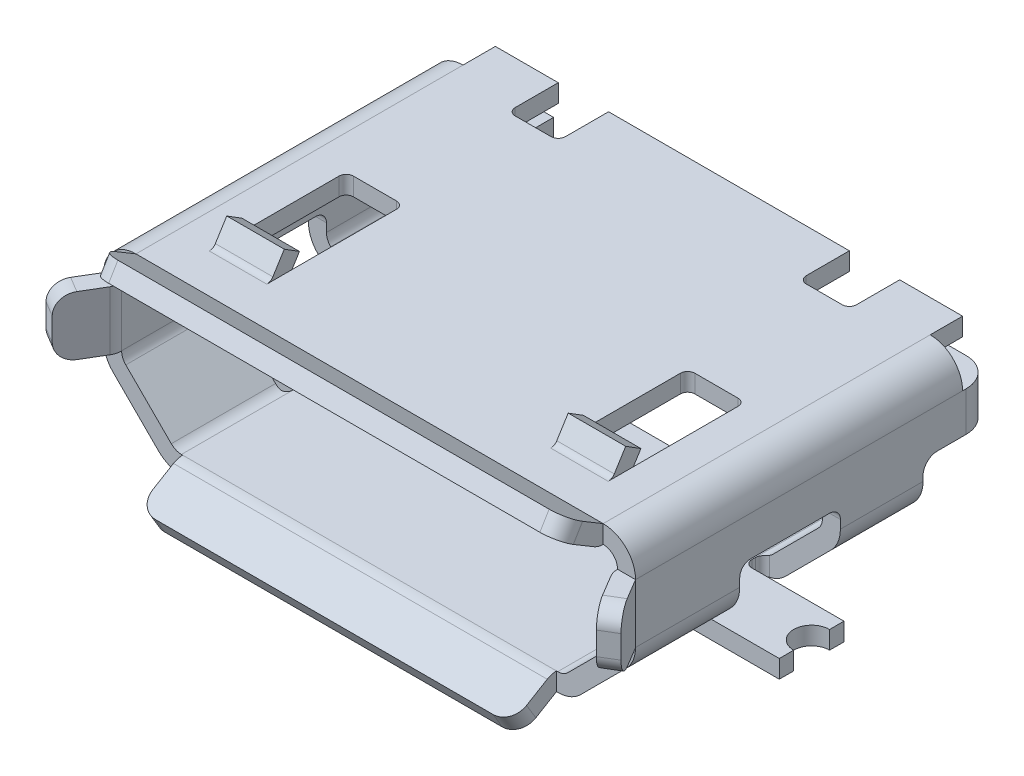
SolidWorks part; units mm, degrees
material "Pure Silver"
ref_plane "Front Plane" through (0, 0, 0) normal (0, 0, 1) x (1, 0, 0)
ref_plane "Top Plane" through (0, 0, 0) normal (0, 1, 0) x (1, 0, 0)
ref_plane "Right Plane" through (0, 0, 0) normal (1, 0, 0) x (0, 0, -1)
sketch "Sketch1" plane through (0, 0, 0) normal (0, 0, 1) x (1, 0, 0)
  line L0 (0, 0) -> (2.6172, 0)
  line L1 (55, 0) -> (-55, 0) construction
  line L2 (2.7586, 0.0586) -> (3.3914, 0.6914)
  line L3 (3.45, 0.8328) -> (3.45, 1.65)
  line L4 (3.25, 1.85) -> (-3.25, 1.85)
  line L5 (-3.45, 1.65) -> (-3.45, 0.8328)
  line L6 (-3.3914, 0.6914) -> (-2.7586, 0.0586)
  line L7 (-2.6172, 0) -> (0, 0)
  line L8 (0, -55) -> (0, 55) construction
  arc A0 (-3.25, 1.85) -> (-3.45, 1.65) centre (-3.25, 1.65) ccw
  arc A1 (-3.45, 0.8328) -> (-3.3914, 0.6914) centre (-3.25, 0.8328) ccw
  arc A2 (-2.7586, 0.0586) -> (-2.6172, 0) centre (-2.6172, 0.2) ccw
  arc A3 (2.6172, 0) -> (2.7586, 0.0586) centre (2.6172, 0.2) ccw
  arc A4 (3.3914, 0.6914) -> (3.45, 0.8328) centre (3.25, 0.8328) ccw
  arc A5 (3.45, 1.65) -> (3.25, 1.85) centre (3.25, 1.65) ccw
  point P14 (-3.45, 1.85)
  point P17 (-3.45, 0.75)
  point P20 (-2.7, 0)
  point P23 (2.7, 0)
  point P26 (3.45, 0.75)
  dimension "D7" = 0.2
  dimension "D1" = 6.9
  dimension "D2" = 3.45
  dimension "D3" = 1.85
  dimension "D4" = 1.1
  dimension "D5" = 5.4
  dimension "D6" = 2.7
extrude "Extrude-Thin1" add sketch "Sketch1" against normal blind 5 thin
ref_plane "Plane1" through (0, 1.65, 0) normal (0, 1, 0) x (1, 0, 0)
sketch "Sketch2" plane through (0, 1.65, 0) normal (0, 1, 0) x (1, 0, 0)
  line L0 (-3.7, 0) -> (-4, -0.5017)
  line L1 (-1.2925, 0) -> (1.2925, 0) construction
  line L2 (-3.7, 5) -> (-3.7, 0) construction
  line L3 (-4, -0.5017) -> (-3.7854, -0.63)
  line L4 (-3.7854, -0.63) -> (-3.4854, -0.1283)
  line L5 (-3.45, 0) -> (-3.7, 0)
  line L6 (0, -1.2925) -> (0, 1.2925) construction
  line L7 (3.7, 0) -> (4, -0.5017)
  line L9 (3.7, 5) -> (3.7, 0) construction
  line L10 (4, -0.5017) -> (3.7854, -0.63)
  line L11 (3.7854, -0.63) -> (3.4854, -0.1283)
  line L12 (3.45, 0) -> (3.7, 0)
  arc A0 (-3.4854, -0.1283) -> (-3.45, 0) centre (-3.7, 0) ccw
  arc A1 (3.4854, -0.1283) -> (3.45, 0) centre (3.7, 0) cw
  dimension "D1" = 0.25
  dimension "D2" = 0.63
  dimension "D3" = 4
  dimension "D4" = 0.25
  dimension "D5" = 0.25
  dimension "D6" = 0.63
  dimension "D7" = 4
extrude "Boss-Extrude1" add sketch "Sketch2" against normal blind 0.82
sketch "Sketch3" plane through (0, 0, 0) normal (1, 0, 0) x (0, 0, -1)
  line L0 (0, 2.1) -> (-0.5017, 2.4)
  line L1 (0, 1.6225) -> (0, -1.6225) construction
  line L2 (-0.5017, 2.4) -> (-0.63, 2.1854)
  line L3 (-0.63, 2.1854) -> (-0.1283, 1.8854)
  line L5 (5, 2.1) -> (0, 2.1) construction
  line L6 (0, 2.1) -> (0, 1.85)
  arc A0 (-0.1283, 1.8854) -> (0, 1.85) centre (0, 2.1) ccw
  dimension "D1" = 0.25
  dimension "D2" = 0.63
  dimension "D3" = 0.3
sketch "Sketch4" plane through (0, 0, 0) normal (1, 0, 0) x (0, 0, -1)
  line L0 (0, -0.25) -> (-0.5017, -0.55)
  line L1 (0, 1.6225) -> (0, -1.6225) construction
  line L2 (5, -0.25) -> (0, -0.25) construction
  line L3 (-0.5017, -0.55) -> (-0.63, -0.3354)
  line L4 (-0.63, -0.3354) -> (-0.1283, -0.0354)
  line L5 (0, 0) -> (0, -0.25)
  arc A0 (-0.1283, -0.0354) -> (0, 0) centre (0, -0.25) cw
  dimension "D1" = 0.63
  dimension "D2" = 0.3
extrude "Boss-Extrude2" add sketch "Sketch4" along normal mid plane 5.2
extrude "Boss-Extrude3" add sketch "Sketch3" along normal mid plane 6.5
fillet "Fillet1" radius 0.25 8 edges at (3.8927, 0.83, 0.5658) (3.8927, 1.65, 0.5658) (-3.8927, 0.83, 0.5658) (-3.8927, 1.65, 0.5658) (-2.6, -0.4427, 0.5658) (2.6, -0.4427, 0.5658) (3.25, 2.2927, 0.5658) (-3.25, 2.2927, 0.5658)
sketch "Sketch5" plane through (0, 0, 0) normal (0, 1, 0) x (1, 0, 0)
  line L0 (2.7172, 1.45) -> (3.7, 1.45)
  line L2 (3.7, 5) -> (3.7, 0) construction
  line L3 (3.7, 1.45) -> (3.7, 2.85)
  line L4 (3.7, 2.85) -> (2.7172, 2.85)
  line L5 (2.6172, 2.75) -> (2.6172, 1.55)
  line L6 (-3.7, 2.85) -> (-2.7172, 2.85)
  line L7 (-3.7, 5) -> (-3.7, 0) construction
  line L8 (-2.6172, 2.75) -> (-2.6172, 1.55)
  line L10 (-2.7172, 1.45) -> (-3.7, 1.45)
  line L11 (-3.7, 2.85) -> (-3.7, 1.45)
  line L12 (2.6172, 2.15) -> (3.7, 2.15) construction
  line L13 (-1.6225, 0) -> (1.6225, 0) construction
  line L14 (-2.6172, 5) -> (-2.6172, 0) construction
  line L15 (2.6172, 5) -> (2.6172, 0) construction
  arc A0 (-2.6172, 2.75) -> (-2.7172, 2.85) centre (-2.7172, 2.75) ccw
  arc A1 (2.7172, 1.45) -> (2.6172, 1.55) centre (2.7172, 1.55) cw
  arc A2 (2.7172, 2.85) -> (2.6172, 2.75) centre (2.7172, 2.75) ccw
  arc A3 (-2.6172, 1.55) -> (-2.7172, 1.45) centre (-2.7172, 1.55) cw
  dimension "D3" = 0.1
  dimension "D1" = 2.15
  dimension "D2" = 1.4
extrude "Cut-Extrude1" cut sketch "Sketch5" along normal blind 1.1 and the other way through all
fillet "Fillet2" radius 0.15 4 edges at (3.575, 1.1, -1.45) (3.575, 1.1, -2.85) (-3.575, 1.1, -2.85) (-3.575, 1.1, -1.45)
sketch "Sketch6" plane through (0, -0.25, 0) normal (0, -1, 0) x (1, 0, 0)
  line L0 (0, -1.6225) -> (0, 1.6225) construction
  line L1 (-4, -1.7) -> (4, -1.7)
  line L2 (-4, -1.7) -> (-4, -1.9)
  line L3 (-4, -2.6) -> (4, -2.6)
  line L4 (4, -1.7) -> (4, -1.9)
  line L5 (-4, -2.15) -> (4, -2.15) construction
  line L6 (1.6225, 0) -> (-1.6225, 0) construction
  line L7 (-4, -2.4) -> (-4, -2.6)
  line L8 (4, -2.4) -> (4, -2.6)
  arc A0 (-4, -2.4) -> (-4, -1.9) centre (-4, -2.15) ccw
  arc A1 (4, -1.9) -> (4, -2.4) centre (4, -2.15) ccw
  dimension "D5" = 0.5
  dimension "D1" = 8
  dimension "D2" = 4
  dimension "D3" = 2.15
  dimension "D4" = 0.9
extrude "Boss-Extrude4" add sketch "Sketch6" against normal blind 0.25
fillet "Fillet3" radius 0.1 4 edges at (2.6172, -0.125, -2.6) (2.6172, -0.125, -1.7) (-2.6172, -0.125, -1.7) (-2.6172, -0.125, -2.6)
sketch "Sketch7" plane through (0, 2.1, 0) normal (0, 1, 0) x (1, 0, 0)
  line L0 (-1.6225, 0) -> (1.6225, 0) construction
  line L1 (-2.675, 2.45) -> (-2.075, 2.45)
  line L2 (-2.775, 2.35) -> (-2.775, 0.6)
  line L3 (-2.775, 0.6) -> (-1.975, 0.6)
  line L4 (-1.975, 2.35) -> (-1.975, 0.6)
  line L5 (2.075, 2.45) -> (2.675, 2.45)
  line L6 (1.975, 2.35) -> (1.975, 0.6)
  line L7 (1.975, 0.6) -> (2.775, 0.6)
  line L8 (2.775, 2.35) -> (2.775, 0.6)
  line L9 (-2.375, 2.45) -> (-2.375, 0.6) construction
  line L10 (2.375, 2.45) -> (2.375, 0.6) construction
  line L11 (0, -1.6225) -> (0, 1.6225) construction
  arc A0 (2.675, 2.45) -> (2.775, 2.35) centre (2.675, 2.35) cw
  arc A1 (2.075, 2.45) -> (1.975, 2.35) centre (2.075, 2.35) ccw
  arc A2 (-2.675, 2.45) -> (-2.775, 2.35) centre (-2.675, 2.35) ccw
  arc A3 (-1.975, 2.35) -> (-2.075, 2.45) centre (-2.075, 2.35) ccw
  dimension "D1" = 0.1
  dimension "D2" = 0.6
  dimension "D3" = 4.75
  dimension "D4" = 2.375
  dimension "D5" = 0.8
  dimension "D6" = 2.45
extrude "Cut-Extrude2" cut sketch "Sketch7" against normal blind 0.25
sketch "Sketch9" plane through (-1.975, 0, 0) normal (-1, 0, 0) x (0, 0, 1)
  line L0 (-0.6, 2.1) -> (-0.7882, 2.4)
  line L1 (-0.7882, 2.4) -> (-1, 2.2671)
  line L2 (-1, 2.2671) -> (-0.8118, 1.9671)
  line L3 (-5, 1.85) -> (0, 1.85) construction
  line L4 (-0.6, 1.85) -> (-0.6, 2.1)
  line L7 (0, -1.6225) -> (0, 1.6225) construction
  line L8 (-0.6, 2.1) -> (-2.35, 2.1) construction
  arc A0 (-0.8118, 1.9671) -> (-0.6, 1.85) centre (-0.6, 2.1) ccw
  dimension "D1" = 1
  dimension "D2" = 0.3
extrude "Boss-Extrude5" add sketch "Sketch9" along normal blind 0.8
mirror "Mirror1" about plane through (0, 0, 0) normal (1, 0, 0) of "Boss-Extrude5"
fillet "Fillet4" radius 0.1 2 edges at (2.375, 2.1, -0.6) (-2.375, 2.1, -0.6)
sketch "Sketch10" plane through (0, 0, 0) normal (1, 0, 0) x (0, 0, -1)
  line L0 (5, -0.25) -> (2.75, -0.25) construction
  line L1 (4, -0.25) -> (5, -0.25)
  line L2 (4, -0.25) -> (4, 0.9)
  line L3 (4.2, 1.1) -> (5, 1.1)
  line L4 (5, -0.25) -> (5, 1.1)
  line L5 (5, 0.8328) -> (5, 1.65) construction
  line L6 (1.6, 1.1) -> (2.7, 1.1) construction
  line L7 (0, 1.6225) -> (0, -1.6225) construction
  arc A0 (4.2, 1.1) -> (4, 0.9) centre (4.2, 0.9) ccw
  dimension "D2" = 0.2
  dimension "D1" = 4
extrude "Cut-Extrude3" cut sketch "Sketch10" against normal through all both and the other way through all
sketch "Sketch11" plane through (0, 2.1, 0) normal (0, 1, 0) x (1, 0, 0)
  line L0 (-3.7, 5) -> (-3.7, 0) construction
  line L1 (-3.25, 5) -> (-3.7, 5)
  line L2 (-3.25, 5) -> (-3.25, 4.55)
  line L3 (-3.25, 4.55) -> (-3.7, 4.55)
  line L4 (-3.7, 5) -> (-3.7, 4.55)
  line L5 (3.7, 5) -> (3.7, 0) construction
  line L6 (3.25, 5) -> (3.7, 5)
  line L7 (3.25, 5) -> (3.25, 4.55)
  line L8 (3.25, 4.55) -> (3.7, 4.55)
  line L9 (3.7, 5) -> (3.7, 4.55)
extrude "Cut-Extrude4" cut sketch "Sketch11" against normal through all both and the other way through all
sketch "Sketch12" plane through (0, -0.25, 0) normal (0, -1, 0) x (1, 0, 0)
  line L0 (-2.6172, -4) -> (2.6172, -4) construction
  line L1 (-2.05, -3.5) -> (2.05, -3.5)
  line L2 (-2.25, -3.7) -> (-2.25, -4)
  line L3 (-2.25, -4) -> (2.25, -4)
  line L4 (2.25, -3.7) -> (2.25, -4)
  line L5 (0, -1.6225) -> (0, 1.6225) construction
  line L6 (1.6225, 0) -> (-1.6225, 0) construction
  arc A0 (2.05, -3.5) -> (2.25, -3.7) centre (2.05, -3.7) cw
  arc A1 (-2.05, -3.5) -> (-2.25, -3.7) centre (-2.05, -3.7) ccw
  dimension "D4" = 0.2
  dimension "D1" = 4.5
  dimension "D2" = 2.25
  dimension "D3" = 3.5
extrude "Cut-Extrude5" cut sketch "Sketch12" against normal blind 0.8
fillet "Fillet5" radius 0.1 2 edges at (-2.25, -0.125, -4) (2.25, -0.125, -4)
sketch "Sketch13" plane through (0, 2.1, 0) normal (0, 1, 0) x (1, 0, 0)
  line L0 (3.25, 5) -> (-3.25, 5) construction
  line L1 (-2.375, 5) -> (-1.675, 5)
  line L2 (-2.375, 5) -> (-2.375, 4.4)
  line L3 (-2.275, 4.3) -> (-1.775, 4.3)
  line L4 (-1.675, 5) -> (-1.675, 4.4)
  line L5 (0, -1.6225) -> (0, 1.6225) construction
  line L6 (1.675, 5) -> (2.375, 5)
  line L7 (1.675, 5) -> (1.675, 4.4)
  line L8 (1.775, 4.3) -> (2.275, 4.3)
  line L9 (2.375, 5) -> (2.375, 4.4)
  arc A0 (2.275, 4.3) -> (2.375, 4.4) centre (2.275, 4.4) ccw
  arc A1 (1.675, 4.4) -> (1.775, 4.3) centre (1.775, 4.4) ccw
  arc A2 (-1.775, 4.3) -> (-1.675, 4.4) centre (-1.775, 4.4) ccw
  arc A3 (-2.375, 4.4) -> (-2.275, 4.3) centre (-2.275, 4.4) ccw
  point P14 (2.375, 4.3)
  point P17 (1.675, 4.3)
  point P22 (-2.375, 4.3)
  dimension "D5" = 0.1
  dimension "D1" = 2.375
  dimension "D2" = 2.375
  dimension "D3" = 0.7
  dimension "D4" = 0.7
extrude "Cut-Extrude6" cut sketch "Sketch13" against normal blind 0.8
sketch "Sketch14" plane through (0, 1.65, 0) normal (0, 1, 0) x (1, 0, 0)
  line L0 (-3.7, 4.55) -> (-3.7, 4.6)
  line L1 (-3.3, 5) -> (-2.44, 5)
  line L2 (-2.44, 5) -> (-2.44, 4.75)
  line L3 (-2.44, 4.75) -> (-3.3, 4.75)
  line L4 (-1.6225, 0) -> (1.6225, 0) construction
  line L5 (-3.7, 4.55) -> (-3.7, 0) construction
  line L6 (-3.7, 4.55) -> (-3.45, 4.55)
  line L7 (-3.25, 4.55) -> (-3.7, 4.55) construction
  line L8 (-3.45, 4.55) -> (-3.45, 4.6)
  arc A0 (-3.7, 4.6) -> (-3.3, 5) centre (-3.3, 4.6) cw
  arc A1 (-3.45, 4.6) -> (-3.3, 4.75) centre (-3.3, 4.6) cw
  dimension "D5" = 0.15
  dimension "D1" = 0.25
  dimension "D2" = 5
  dimension "D3" = 1.26
  dimension "D4" = 0.4
extrude "Boss-Extrude6" add sketch "Sketch14" against normal blind 0.55
mirror "Mirror2" about plane through (0, 0, 0) normal (1, 0, 0) of "Boss-Extrude6"
